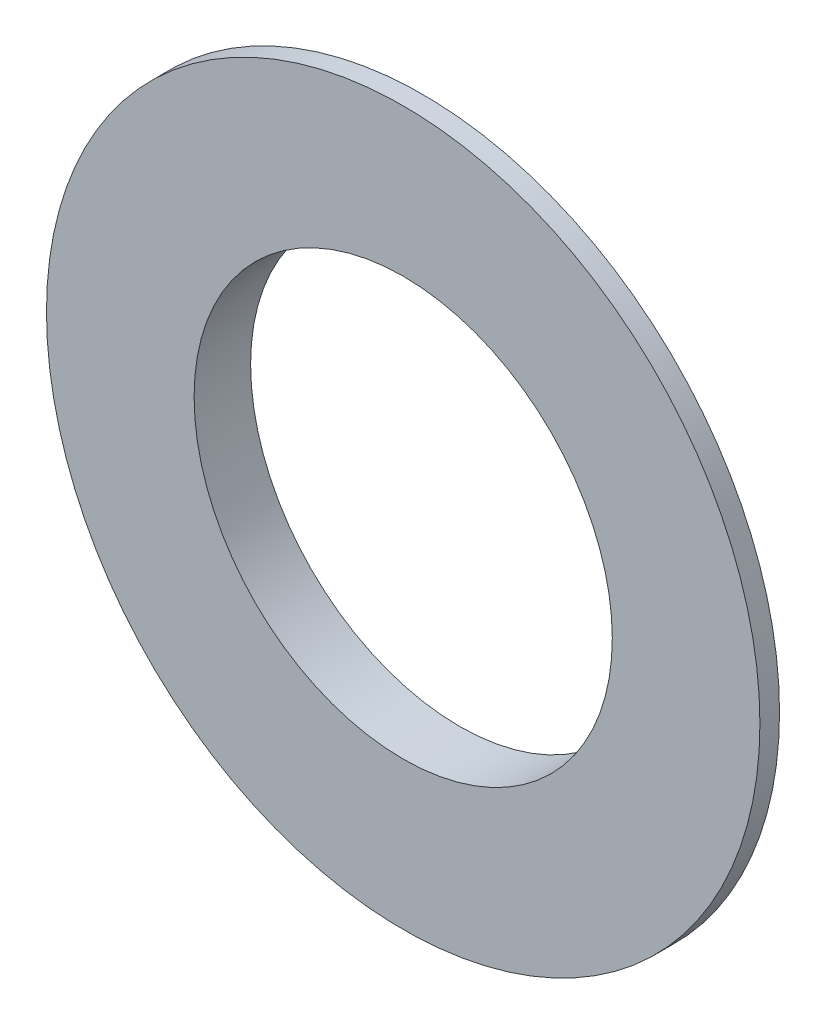
SolidWorks part; units mm, degrees
ref_plane "Front Plane" through (0, 0, 0) normal (0, 0, 1) x (1, 0, 0)
ref_plane "Top Plane" through (0, 0, 0) normal (0, 1, 0) x (1, 0, 0)
ref_plane "Right Plane" through (0, 0, 0) normal (1, 0, 0) x (0, 0, -1)
sketch "Sketch1" plane through (0, 0, 0) normal (0, 1, 0) x (1, 0, 0)
  line L0 (0, 0) -> (-28.8163, 0) construction
  line L1 (-18.9367, 0) -> (-18.9367, 1.0408)
  line L2 (-18.9367, 1.0408) -> (-11.1, 3)
  line L3 (-11.1, 3) -> (-11.1, 0)
  line L4 (-11.1, 0) -> (-18.9367, 0)
  line L5 (0, 0) -> (0, 8.353) construction
  dimension "D1" = 3
  dimension "D2" = 11.1
revolve "Revolve1" add sketch "Sketch1" angle 360 about L5
